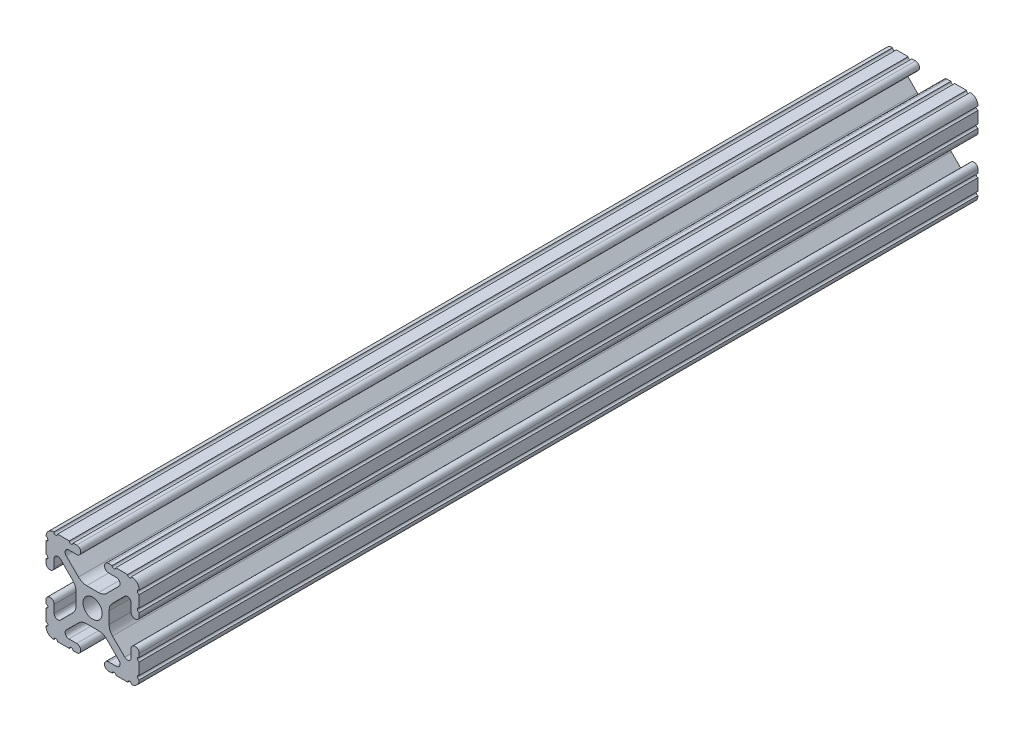
SolidWorks part; units mm, degrees
ref_plane "Front Plane" through (0, 0, 0) normal (0, 0, 1) x (1, 0, 0)
ref_plane "Top Plane" through (0, 0, 0) normal (0, 1, 0) x (1, 0, 0)
ref_plane "Right Plane" through (0, 0, 0) normal (1, 0, 0) x (0, 0, -1)
ref_plane "Plane1" through (0, 0, -342.9) normal (0, 0, -1) x (-1, 0, 0)
sketch "Sketch1" plane through (0, 0, -342.9) normal (0, 0, -1) x (-1, 0, 0)
  line L0 (12.7, -9.5504) -> (12.7, -6.3331)
  line L1 (12.7, -5.3171) -> (12.7, -4.3434)
  line L2 (10.4902, -4.3434) -> (10.4902, -6.4748)
  line L3 (8.7558, -7.1932) -> (5.4257, -3.8632)
  line L4 (4.4958, -1.6181) -> (4.4958, 1.6181)
  line L5 (5.4257, 3.8632) -> (8.7558, 7.1932)
  line L6 (10.4902, 6.4748) -> (10.4902, 4.3434)
  line L7 (12.7, 4.3434) -> (12.7, 5.3171)
  line L8 (12.7, 6.3331) -> (12.7, 9.5504)
  line L9 (9.5504, 12.7) -> (6.3331, 12.7)
  line L10 (5.3171, 12.7) -> (4.3434, 12.7)
  line L11 (4.3434, 10.4902) -> (6.4748, 10.4902)
  line L12 (7.1932, 8.7558) -> (3.8632, 5.4257)
  line L13 (1.6181, 4.4958) -> (-1.6181, 4.4958)
  line L14 (-3.8632, 5.4257) -> (-7.1932, 8.7558)
  line L15 (-6.4748, 10.4902) -> (-4.3434, 10.4902)
  line L16 (-4.3434, 12.7) -> (-5.3171, 12.7)
  line L17 (-6.3331, 12.7) -> (-9.5504, 12.7)
  line L18 (-12.7, 9.5504) -> (-12.7, 6.3331)
  line L19 (-12.7, 5.3171) -> (-12.7, 4.3434)
  line L20 (-10.4902, 4.3434) -> (-10.4902, 6.4748)
  line L21 (-8.7558, 7.1932) -> (-5.4257, 3.8632)
  line L22 (-4.4958, 1.6181) -> (-4.4958, -1.6181)
  line L23 (-5.4257, -3.8632) -> (-8.7558, -7.1932)
  line L24 (-10.4902, -6.4748) -> (-10.4902, -4.3434)
  line L25 (-12.7, -4.3434) -> (-12.7, -5.3171)
  line L26 (-12.7, -6.3331) -> (-12.7, -9.5504)
  line L27 (-9.5504, -12.7) -> (-6.3331, -12.7)
  line L28 (-5.3171, -12.7) -> (-4.3434, -12.7)
  line L29 (-4.3434, -10.4902) -> (-6.4748, -10.4902)
  line L30 (-7.1932, -8.7558) -> (-3.8632, -5.4257)
  line L31 (-1.6181, -4.4958) -> (1.6181, -4.4958)
  line L32 (3.8632, -5.4257) -> (7.1932, -8.7558)
  line L33 (6.4748, -10.4902) -> (4.3434, -10.4902)
  line L34 (4.3434, -12.7) -> (5.3171, -12.7)
  line L35 (6.3331, -12.7) -> (9.5504, -12.7)
  arc A0 (12.6998, -10.5664) -> (12.7, -9.5504) centre (12.7, -10.0584) cw
  arc A1 (12.7, -6.3331) -> (12.7, -5.3171) centre (12.7, -5.8251) cw
  arc A2 (12.7, -4.3434) -> (10.4902, -4.3434) centre (11.5951, -4.3434) ccw
  arc A3 (10.4902, -6.4748) -> (8.7558, -7.1932) centre (9.4742, -6.4748) cw
  arc A4 (5.4257, -3.8632) -> (4.4958, -1.6181) centre (7.6708, -1.6181) cw
  arc A5 (4.4958, 1.6181) -> (5.4257, 3.8632) centre (7.6708, 1.6181) cw
  arc A6 (8.7558, 7.1932) -> (10.4902, 6.4748) centre (9.4742, 6.4748) cw
  arc A7 (10.4902, 4.3434) -> (12.7, 4.3434) centre (11.5951, 4.3434) ccw
  arc A8 (12.7, 5.3171) -> (12.7, 6.3331) centre (12.7, 5.8251) cw
  arc A9 (12.7, 9.5504) -> (12.6998, 10.5664) centre (12.7, 10.0584) cw
  arc A10 (12.6998, 10.5664) -> (10.5664, 12.6998) centre (10.5918, 10.5918) ccw
  arc A11 (10.5664, 12.6998) -> (9.5504, 12.7) centre (10.0584, 12.7) cw
  arc A12 (6.3331, 12.7) -> (5.3171, 12.7) centre (5.8251, 12.7) cw
  arc A13 (4.3434, 12.7) -> (4.3434, 10.4902) centre (4.3434, 11.5951) ccw
  arc A14 (6.4748, 10.4902) -> (7.1932, 8.7558) centre (6.4748, 9.4742) cw
  arc A15 (3.8632, 5.4257) -> (1.6181, 4.4958) centre (1.6181, 7.6708) cw
  arc A16 (-1.6181, 4.4958) -> (-3.8632, 5.4257) centre (-1.6181, 7.6708) cw
  arc A17 (-7.1932, 8.7558) -> (-6.4748, 10.4902) centre (-6.4748, 9.4742) cw
  arc A18 (-4.3434, 10.4902) -> (-4.3434, 12.7) centre (-4.3434, 11.5951) ccw
  arc A19 (-5.3171, 12.7) -> (-6.3331, 12.7) centre (-5.8251, 12.7) cw
  arc A20 (-9.5504, 12.7) -> (-10.5664, 12.6998) centre (-10.0584, 12.7) cw
  arc A21 (-10.5664, 12.6998) -> (-12.6998, 10.5664) centre (-10.5918, 10.5918) ccw
  arc A22 (-12.6998, 10.5664) -> (-12.7, 9.5504) centre (-12.7, 10.0584) cw
  arc A23 (-12.7, 6.3331) -> (-12.7, 5.3171) centre (-12.7, 5.8251) cw
  arc A24 (-12.7, 4.3434) -> (-10.4902, 4.3434) centre (-11.5951, 4.3434) ccw
  arc A25 (-10.4902, 6.4748) -> (-8.7558, 7.1932) centre (-9.4742, 6.4748) cw
  arc A26 (-5.4257, 3.8632) -> (-4.4958, 1.6181) centre (-7.6708, 1.6181) cw
  arc A27 (-4.4958, -1.6181) -> (-5.4257, -3.8632) centre (-7.6708, -1.6181) cw
  arc A28 (-8.7558, -7.1932) -> (-10.4902, -6.4748) centre (-9.4742, -6.4748) cw
  arc A29 (-10.4902, -4.3434) -> (-12.7, -4.3434) centre (-11.5951, -4.3434) ccw
  arc A30 (-12.7, -5.3171) -> (-12.7, -6.3331) centre (-12.7, -5.8251) cw
  arc A31 (-12.7, -9.5504) -> (-12.6998, -10.5664) centre (-12.7, -10.0584) cw
  arc A32 (-12.6998, -10.5664) -> (-10.5664, -12.6998) centre (-10.5918, -10.5918) ccw
  arc A33 (-10.5664, -12.6998) -> (-9.5504, -12.7) centre (-10.0584, -12.7) cw
  arc A34 (-6.3331, -12.7) -> (-5.3171, -12.7) centre (-5.8251, -12.7) cw
  arc A35 (-4.3434, -12.7) -> (-4.3434, -10.4902) centre (-4.3434, -11.5951) ccw
  arc A36 (-6.4748, -10.4902) -> (-7.1932, -8.7558) centre (-6.4748, -9.4742) cw
  arc A37 (-3.8632, -5.4257) -> (-1.6181, -4.4958) centre (-1.6181, -7.6708) cw
  arc A38 (1.6181, -4.4958) -> (3.8632, -5.4257) centre (1.6181, -7.6708) cw
  arc A39 (7.1932, -8.7558) -> (6.4748, -10.4902) centre (6.4748, -9.4742) cw
  arc A40 (4.3434, -10.4902) -> (4.3434, -12.7) centre (4.3434, -11.5951) ccw
  arc A41 (5.3171, -12.7) -> (6.3331, -12.7) centre (5.8251, -12.7) cw
  arc A42 (9.5504, -12.7) -> (10.5664, -12.6998) centre (10.0584, -12.7) cw
  arc A43 (10.5664, -12.6998) -> (12.6998, -10.5664) centre (10.5918, -10.5918) ccw
  circle A44 centre (0, 0) radius 2.6035
extrude "Boss-Extrude1" add sketch "Sketch1" against normal blind 228.6
